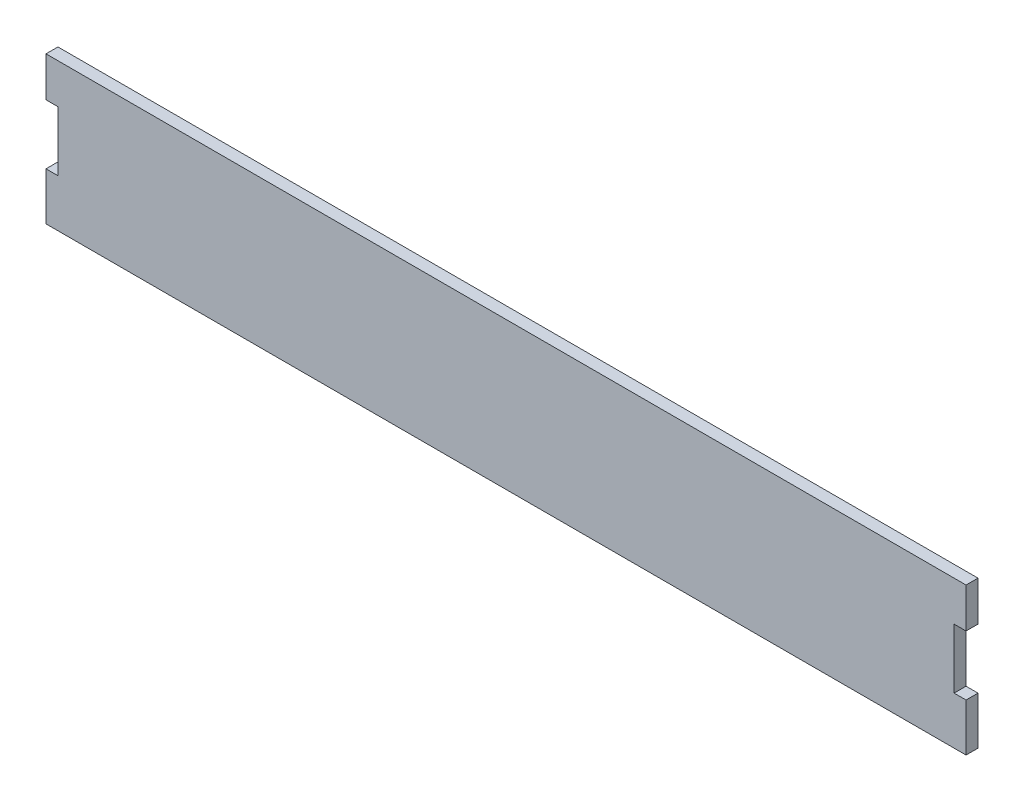
SolidWorks part; units mm, degrees
ref_plane "Front Plane" through (0, 0, 0) normal (0, 0, 1) x (1, 0, 0)
ref_plane "Top Plane" through (0, 0, 0) normal (0, 1, 0) x (1, 0, 0)
ref_plane "Right Plane" through (0, 0, 0) normal (1, 0, 0) x (0, 0, -1)
sketch "Sketch1" plane through (0, 0, 0) normal (0, 0, 1) x (1, 0, 0)
  line L0 (-113.5, 8.5934) -> (-116.5, 8.5934)
  line L1 (-113.5, 18.5934) -> (111.5, 18.5934)
  line L3 (-110.2393, -18.3831) -> (112.2167, -18.3831)
  line L5 (-113.5, 18.5934) -> (112.2167, -18.3831) construction
  line L6 (-110.2393, -18.3831) -> (111.5, 18.5934) construction
  line L8 (-116.5, -6.4066) -> (-113.5, -6.4066)
  line L10 (111.5, 8.5934) -> (114.5, 8.5934)
  line L12 (114.5, -6.4066) -> (111.5, -6.4066)
  line L14 (111.5, 8.5934) -> (111.5, -6.4066)
  line L15 (114.5, -6.4066) -> (114.5, -18.3831)
  line L16 (114.5, -18.3831) -> (112.2167, -18.3831)
  line L17 (111.5, 18.5934) -> (114.5, 18.5934)
  line L18 (114.5, 18.5934) -> (114.5, 8.5934)
  line L19 (-113.5, 18.5934) -> (-116.5, 18.5934)
  line L20 (-116.5, 18.5934) -> (-116.5, 8.5934)
  line L21 (-116.5, -6.4066) -> (-116.5, -18.3831)
  line L22 (-116.5, -18.3831) -> (-110.2393, -18.3831)
  line L23 (-113.5, 8.5934) -> (-113.5, -6.4066)
  point P0 (0, 0)
  dimension "D2" = 225
  dimension "D3" = 10
  dimension "D4" = 15
  dimension "D5" = 3
  dimension "D6" = 15
  dimension "D7" = 3
  dimension "D8" = 3
  dimension "D9" = 3
  dimension "D10" = 3
  dimension "D11" = 3
  dimension "D12" = 36.9765
extrude "Boss-Extrude1" add sketch "Sketch1" along normal blind 3
